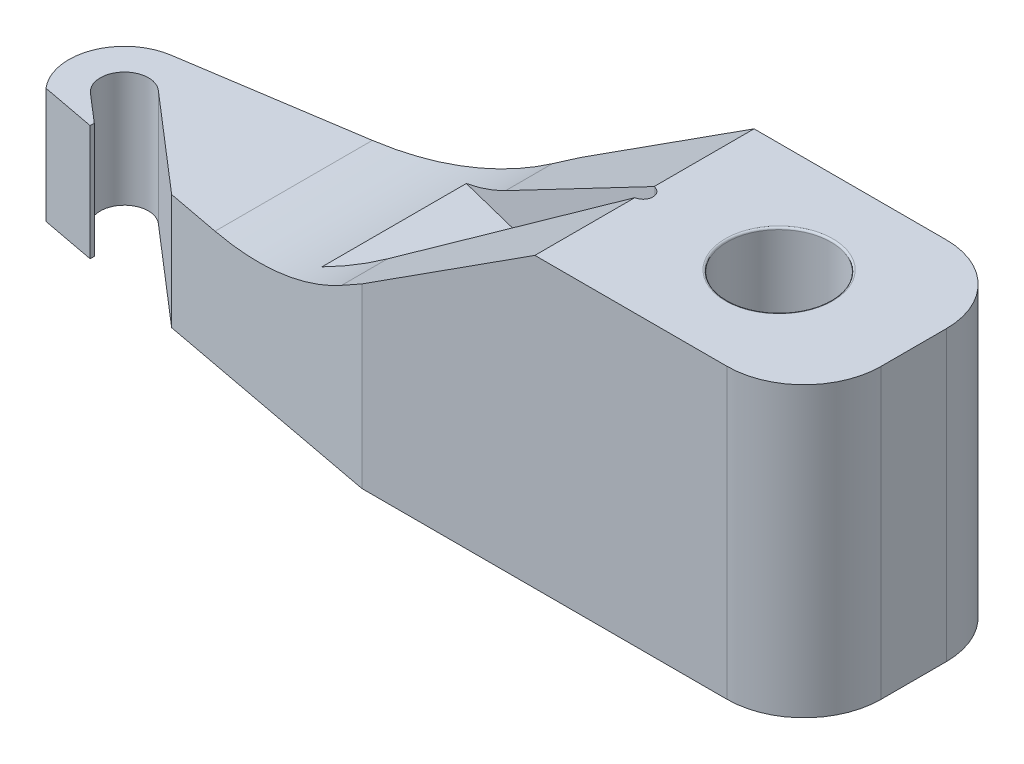
SolidWorks part; units mm, degrees
ref_plane "Front Plane" through (0, 0, 0) normal (0, 0, 1) x (1, 0, 0)
ref_plane "Top Plane" through (0, 0, 0) normal (0, 1, 0) x (1, 0, 0)
ref_plane "Right Plane" through (0, 0, 0) normal (1, 0, 0) x (0, 0, -1)
sketch "Sketch1" plane through (0, 0, 0) normal (0, 1, 0) x (1, 0, 0)
  line L0 (0.7, 0.57) -> (-1.6, 0.57)
  line L1 (0.7, 0.57) -> (0.7, -0.57)
  line L2 (0.7, -0.57) -> (-1.6, -0.57)
  line L3 (-1.6, 0.57) -> (-3.681, 0.25)
  line L4 (-3.4049, 0) -> (-2.2666, -0.982) construction
  line L5 (-1.6, -0.57) -> (-3.7439, -0.166)
  line L6 (0, 0) -> (-4.3932, 0) construction
  line L7 (-3.3232, 0.0948) -> (-2.1848, -0.8872)
  line L8 (-3.4867, -0.0948) -> (-2.3484, -1.0768)
  line L9 (-3.341, 0) -> (-3.341, -0.5283)
  line L13 (1.2, 1.1) -> (1.2, -1.1)
  circle A0 centre (0, 0) radius 0.27
  circle A1 centre (-3.7, 0) radius 0.1717
  arc A2 (-3.3232, 0.0948) -> (-3.4867, -0.0948) centre (-3.4049, 0) ccw
  arc A3 (-2.3484, -1.0768) -> (-2.1848, -0.8872) centre (-2.2666, -0.982) ccw
  circle A4 centre (-3.4049, 0) radius 0.2891
  point P13 (-2.8358, -0.491)
  dimension "D1" = 0.57
  dimension "D9" = 0.54
  dimension "D2" = 0.57
  dimension "D3" = 0.7
  dimension "D4" = 1.6
  dimension "D5" = 1.6
  dimension "D6" = 0.25
  dimension "D12" = 0.5
extrude "Boss-Extrude1" add sketch "Sketch1" along normal blind 1.5
pattern_linear "LPattern1" [suppressed] count 9 spacing 3.2 count 4 spacing 6.2
sketch "Sketch2" plane through (0, 0, 0) normal (0, 0, 1) x (1, 0, 0)
  line L0 (-4.2545, 0.6) -> (-2.1, 0.6)
  line L1 (-2.1, 0.6) -> (-0.7, 1.5)
  line L2 (-0.7, 1.5) -> (-4.2545, 1.5)
  line L3 (-4.2545, 1.5) -> (-4.2545, 0.6)
  line L4 (0.7, 1.5) -> (0.7, 0) construction
  line L5 (-1.6, 0) -> (-2.8188, 0) construction
  dimension "D1" = 0.6
  dimension "D2" = 1.4
  dimension "D3" = 2.8
extrude "Cut-Extrude1" cut sketch "Sketch2" against normal through all and the other way through all
fillet "Fillet1" radius 0.01 2 edges at (0, 1.5, 0.27) (0, 0, 0.27)
fillet "Fillet2" radius 1.5 1 edges at (-2.1, 0.6, -0.0087)
fillet "Fillet3" radius 0.4 2 edges at (0.7, 0.75, -0.57) (0.7, 0.75, 0.57)
sketch "Sketch4" plane through (0, 1.5, 0) normal (0, 1, 0) x (1, 0, 0)
  line L0 (-0.5, 0) -> (-2.5, 0.5)
  line L2 (-2.5, 0.5) -> (-2.5, -0.5)
  line L3 (-2.5, -0.5) -> (-0.5, 0)
  dimension "D1" = 0.5
  dimension "D2" = 0.5
  dimension "D3" = 0.5
  dimension "D4" = 2.5
extrude "Cut-Extrude2" cut sketch "Sketch4" against normal blind 0.8
fillet "Fillet4" radius 0.05 1 edges at (-0.5, 1.1, 0)
